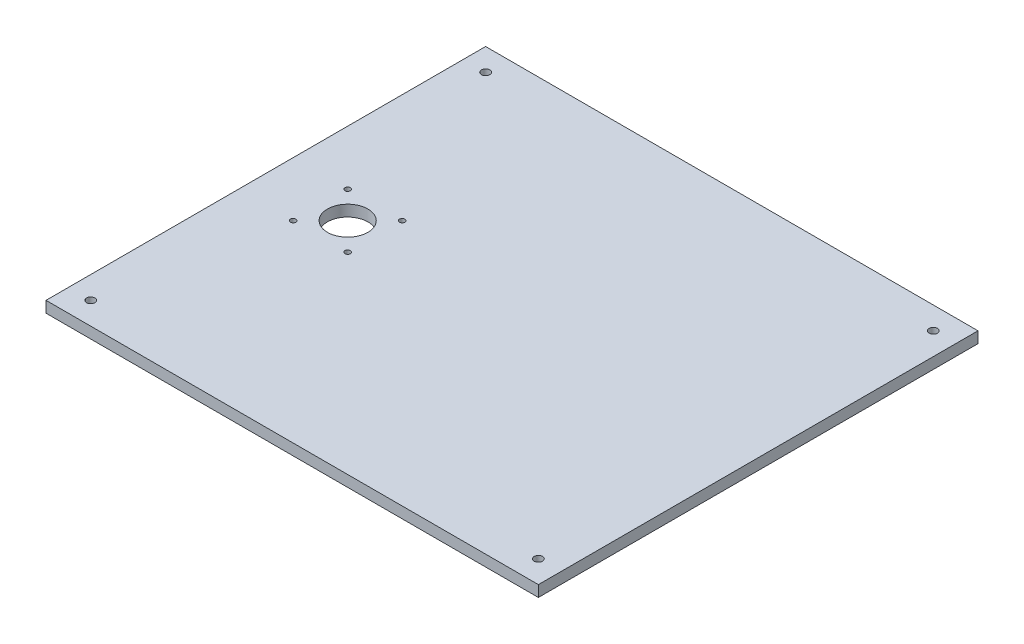
SolidWorks part; units mm, degrees
ref_plane "Front Plane" through (0, 0, 0) normal (0, 0, 1) x (1, 0, 0)
ref_plane "Top Plane" through (0, 0, 0) normal (0, 1, 0) x (1, 0, 0)
ref_plane "Right Plane" through (0, 0, 0) normal (1, 0, 0) x (0, 0, -1)
sketch "Sketch1" plane through (0, 0, 0) normal (0, 1, 0) x (1, 0, 0)
  line L1 (-140, -125) -> (140, -125)
  line L2 (-140, -125) -> (-140, 125)
  line L3 (-140, 125) -> (140, 125)
  line L4 (140, -125) -> (140, 125)
  line L5 (-140, -125) -> (140, 125) construction
  line L6 (-140, 125) -> (140, -125) construction
  point P0 (0, 0)
  dimension "D1" = 280
  dimension "D2" = 250
extrude "Boss-Extrude1" add sketch "Sketch1" along normal blind 6.35
sketch "Sketch3" plane through (0, 6.35, 0) normal (0, 1, 0) x (1, 0, 0)
  line L0 (-140, -125) -> (140, -125) construction
  line L1 (-140, 125) -> (-140, -125) construction
  circle A0 centre (-127.3, -112.3) radius 2.3813
  dimension "D1" = 4.7625
  dimension "D2" = 12.7
  dimension "D3" = 12.7
extrude "Cut-Extrude1" cut sketch "Sketch3" against normal through all
mirror "Mirror1" about plane through (0, 0, 0) normal (0, 0, 1) of "Cut-Extrude1"
mirror "Mirror2" about plane through (0, 0, 0) normal (1, 0, 0) of "Mirror1", "Cut-Extrude1"
sketch "Sketch7" plane through (0, 6.35, 0) normal (0, 1, 0) x (-1, 0, 0)
  line L0 (77.95, -15.5) -> (108.95, -15.5) construction
  line L1 (108.95, -15.5) -> (108.95, 15.5) construction
  line L2 (108.95, 15.5) -> (77.95, 15.5) construction
  line L3 (77.95, 15.5) -> (77.95, -15.5) construction
  line L4 (140, -125) -> (140, 125) construction
  circle A0 centre (77.95, 15.5) radius 1.55
  circle A1 centre (93.45, 0) radius 11.5
  circle A2 centre (108.95, 15.5) radius 1.55
  circle A3 centre (108.95, -15.5) radius 1.55
  circle A4 centre (77.95, -15.5) radius 1.55
  point P10 (93.45, -15.5)
  point P11 (93.45, 0)
  point P13 (108.95, 0)
  point P15 (0, 0)
  dimension "D1" = 3.1
  dimension "D4" = 23
  dimension "D2" = 31
  dimension "D3" = 31
  dimension "D5" = 31.05
extrude "Cut-Extrude4" cut sketch "Sketch7" against normal through all
